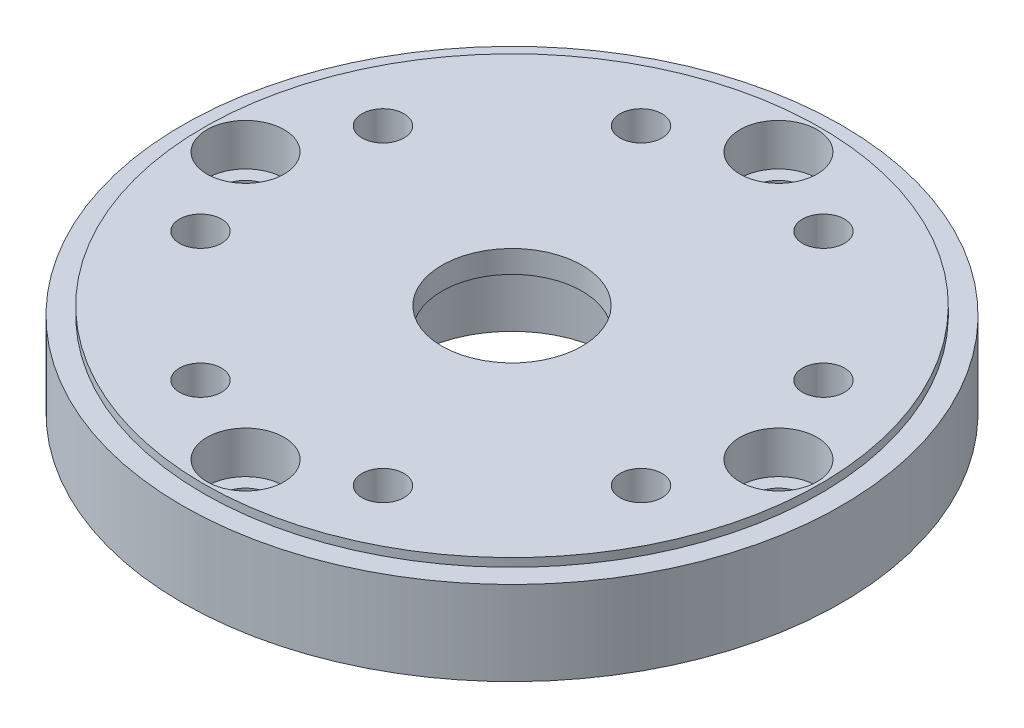
SolidWorks part; units mm, degrees
ref_plane "Front Plane" through (0, 0, 0) normal (0, 0, 1) x (1, 0, 0)
ref_plane "Top Plane" through (0, 0, 0) normal (0, 1, 0) x (1, 0, 0)
ref_plane "Right Plane" through (0, 0, 0) normal (1, 0, 0) x (0, 0, -1)
sketch "Sketch1" plane through (0, 0, 0) normal (0, 1, 0) x (1, 0, 0)
  circle A0 centre (0, 0) radius 7.1
  circle A1 centre (0, 0) radius 23.5
  dimension "D1" = 14.2
  dimension "D2" = 47
extrude "Boss-Extrude1" add sketch "Sketch1" along normal blind 6
sketch "Sketch2" plane through (0, 6, 0) normal (0, 1, 0) x (1, 0, 0)
  circle A2 centre (0, 0) radius 5
  circle A3 centre (0, 0) radius 22
  dimension "D1" = 10
  dimension "D2" = 44
extrude "Boss-Extrude2" add sketch "Sketch2" along normal blind 0.6 and the other way blind 1
sketch "Sketch3" plane through (0, 0, 0) normal (0, -1, 0) x (1, 0, 0)
  circle A0 centre (0, 19) radius 1.75
  circle A1 centre (19, 0) radius 1.75
  circle A2 centre (0, -19) radius 1.75
  circle A3 centre (-19, 0) radius 1.75
  point P12 (0, 0)
  dimension "D1" = 3.5
  dimension "D2" = 19
  dimension "D3" = 4
extrude "Cut-Extrude1" cut sketch "Sketch3" against normal through all
sketch "Sketch4" plane through (0, 0, 0) normal (0, -1, 0) x (-1, 0, 0)
  circle A0 centre (0, 19) radius 1.75 construction
  circle A1 centre (19, 0) radius 1.75 construction
  circle A2 centre (-19, 0) radius 1.75 construction
  circle A3 centre (0, -19) radius 1.75 construction
  circle A4 centre (0, 19) radius 1.75
  circle A5 centre (19, 0) radius 1.75
  circle A6 centre (-19, 0) radius 1.75
  circle A7 centre (0, -19) radius 1.75
  circle A8 centre (0, 19) radius 2.75
  circle A9 centre (19, 0) radius 2.75
  circle A10 centre (-19, 0) radius 2.75
  circle A11 centre (0, -19) radius 2.75
  dimension "D1" = 1
extrude "Cut-Extrude2" cut sketch "Sketch4" along normal blind 3 from surface at -6.6 starting at face at (0, 6.6, 17.25)
sketch "Sketch5" plane through (0, 6.6, 0) normal (0, 1, 0) x (1, 0, 0)
  line L0 (0, 0) -> (0, 24.78) construction
  line L1 (0, 0) -> (-6.5056, 15.706) construction
  circle A0 centre (-6.5056, 15.706) radius 1.5
  circle A1 centre (6.5056, 15.706) radius 1.5
  circle A2 centre (15.706, 6.5056) radius 1.5
  circle A3 centre (15.706, -6.5056) radius 1.5
  circle A4 centre (6.5056, -15.706) radius 1.5
  circle A5 centre (-6.5056, -15.706) radius 1.5
  circle A6 centre (-15.706, -6.5056) radius 1.5
  circle A7 centre (-15.706, 6.5056) radius 1.5
  point P22 (0, 0)
  dimension "D3" = 3
  dimension "D1" = 17
  dimension "D2" = 22.5
  dimension "D4" = 8
extrude "Cut-Extrude3" cut sketch "Sketch5" against normal through all
